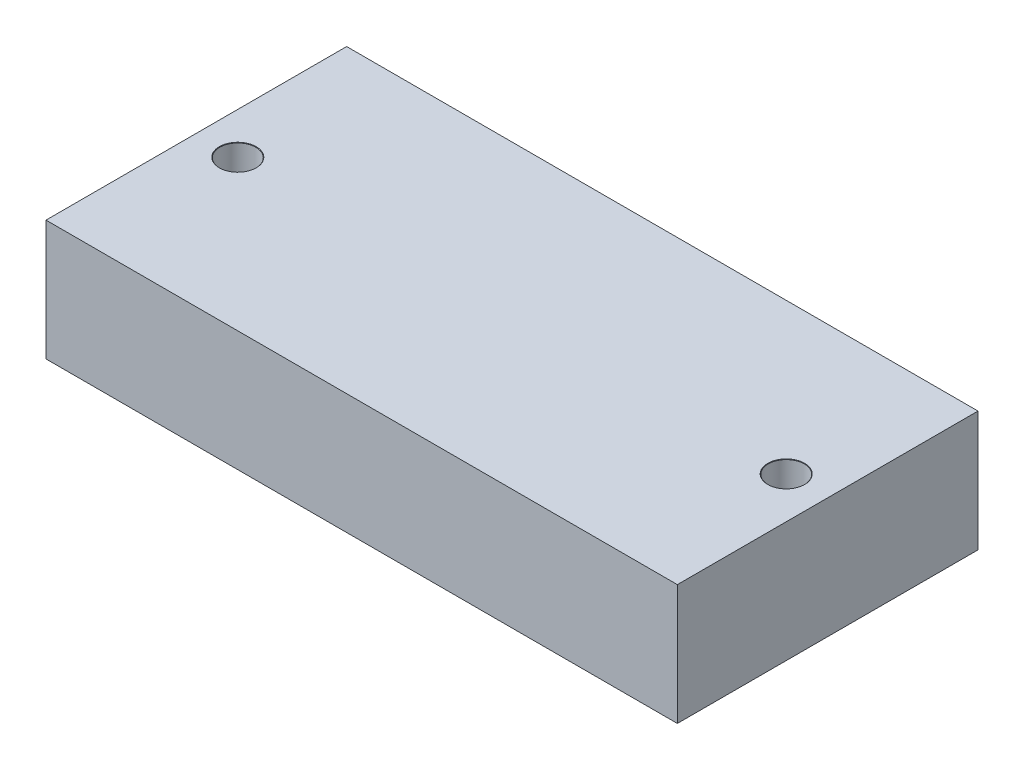
SolidWorks part; units mm, degrees
ref_plane "Front Plane" through (0, 0, 0) normal (0, 0, 1) x (1, 0, 0)
ref_plane "Top Plane" through (0, 0, 0) normal (0, 1, 0) x (1, 0, 0)
ref_plane "Right Plane" through (0, 0, 0) normal (1, 0, 0) x (0, 0, -1)
sketch "Sketch1" plane through (0, 0, 0) normal (0, 1, 0) x (1, 0, 0)
  line L1 (21, 10) -> (-21, 10)
  line L2 (21, 10) -> (21, -10)
  line L3 (21, -10) -> (-21, -10)
  line L4 (-21, 10) -> (-21, -10)
  line L5 (21, 10) -> (-21, -10) construction
  line L6 (21, -10) -> (-21, 10) construction
  point P0 (0, 0)
  dimension "D1" = 20
  dimension "D2" = 42
extrude "Boss-Extrude1" add sketch "Sketch1" along normal blind 8
hole_wizard "M2 Clearance Hole1" positions "Sketch3" profile "Sketch4" hole size "M2" standard "ANSI Metric" end condition through all
sketch "Sketch3" plane through (0, 8, 0) normal (0, 1, 0) x (1, 0, 0)
  line L0 (-18.2425, 0) -> (18.2425, 0) construction
  point P0 (-18.2425, 0)
  point P2 (18.2425, 0)
  point P8 (0, 0)
  dimension "D1" = 36.485
sketch "Sketch4" plane through (-18.2425, 8, 0) normal (1, 0, 0) x (0, 0, 1)
  line L0 (0, 0) -> (0, 8)
  line L1 (0, 8) -> (1.2, 8)
  line L2 (1.2, 8) -> (1.2, 0.025)
  line L3 (1.2, 0.025) -> (1.225, 0)
  line L5 (1.225, 0) -> (0, 0)
  line L6 (-1.2, 0.025) -> (-1.225, 0) construction
  line L11 (0, -6.35) -> (0, 107.95) construction
  dimension "Thru Hole Dia." = 2.4
  dimension "Thru Hole Depth" = 8
  dimension "Near C'Sink Dia." = 2.45
  dimension "Near C'Sink Angle" = 90
